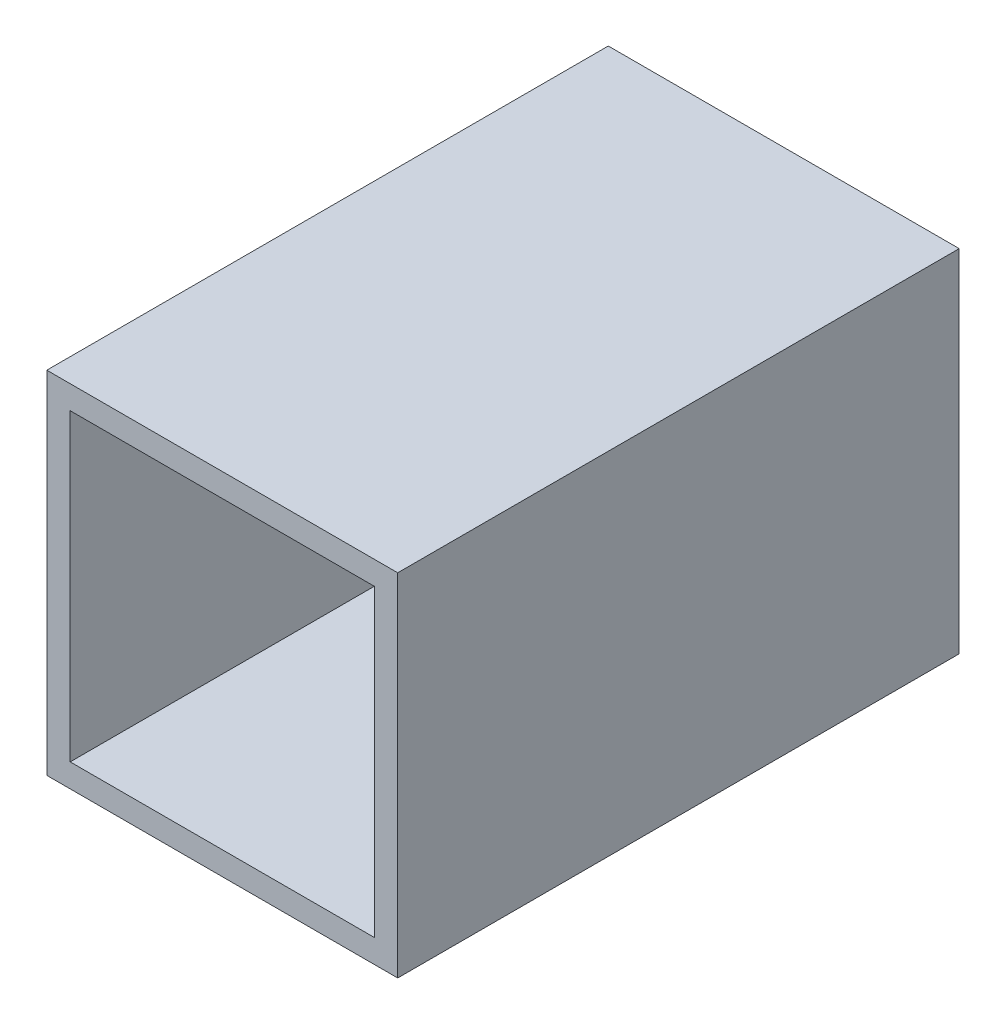
SolidWorks part; units mm, degrees
ref_plane "Front Plane" through (0, 0, 0) normal (0, 0, 1) x (1, 0, 0)
ref_plane "Top Plane" through (0, 0, 0) normal (0, 1, 0) x (1, 0, 0)
ref_plane "Right Plane" through (0, 0, 0) normal (1, 0, 0) x (0, 0, -1)
sketch "Sketch1" plane through (0, 0, 0) normal (0, 0, 1) x (1, 0, 0)
  line L0 (-34.26, 12.591) -> (-1.24, 12.591)
  line L1 (-36.8, 15.131) -> (1.3, 15.131)
  line L2 (-36.8, 15.131) -> (-36.8, -22.969)
  line L3 (-36.8, -22.969) -> (1.3, -22.969)
  line L4 (1.3, 15.131) -> (1.3, -22.969)
  line L5 (-1.24, 12.591) -> (-1.24, -20.429)
  line L6 (-34.26, -20.429) -> (-1.24, -20.429)
  line L7 (-34.26, 12.591) -> (-34.26, -20.429)
  dimension "D1" = 38.1
  dimension "D2" = 38.1
  dimension "D3" = 2.54
extrude "Boss-Extrude1" add sketch "Sketch1" along normal blind 60.96
